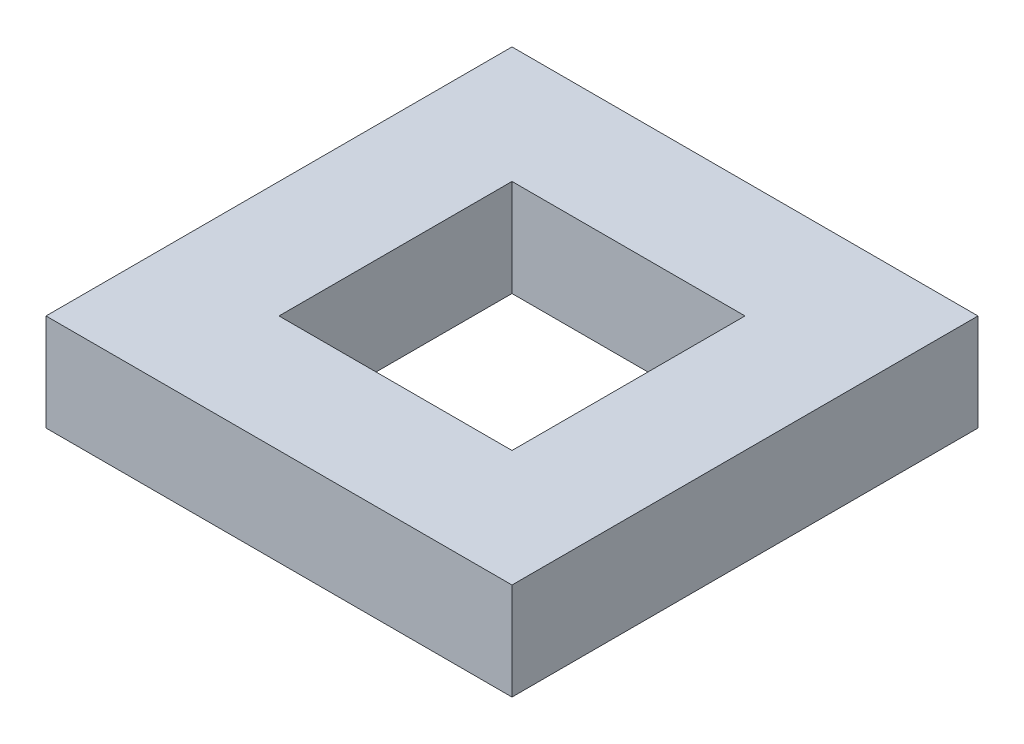
SolidWorks part; units mm, degrees
ref_plane "Front Plane" through (0, 0, 0) normal (0, 0, 1) x (1, 0, 0)
ref_plane "Top Plane" through (0, 0, 0) normal (0, 1, 0) x (1, 0, 0)
ref_plane "Right Plane" through (0, 0, 0) normal (1, 0, 0) x (0, 0, -1)
sketch "Sketch1" plane through (0, 0, 0) normal (0, 1, 0) x (1, 0, 0)
  line L1 (0, 0) -> (15.24, 0)
  line L2 (0, 0) -> (0, 15.24)
  line L3 (0, 15.24) -> (15.24, 15.24)
  line L4 (15.24, 0) -> (15.24, 15.24)
  line L5 (3.81, 3.81) -> (11.43, 3.81)
  line L6 (3.81, 3.81) -> (3.81, 11.43)
  line L7 (3.81, 11.43) -> (11.43, 11.43)
  line L8 (11.43, 3.81) -> (11.43, 11.43)
  dimension "D1" = 15.24
  dimension "D2" = 15.24
  dimension "D3" = 7.62
  dimension "D4" = 7.62
  dimension "D5" = 3.81
  dimension "D6" = 3.81
extrude "Boss-Extrude1" add sketch "Sketch1" along normal blind 3.175
